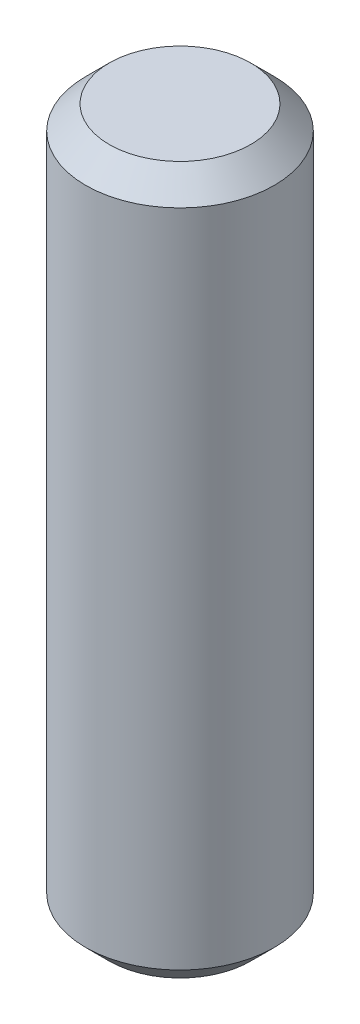
SolidWorks part; units mm, degrees
ref_plane "Front Plane" through (0, 0, 0) normal (0, 0, 1) x (1, 0, 0)
ref_plane "Top Plane" through (0, 0, 0) normal (0, 1, 0) x (1, 0, 0)
ref_plane "Right Plane" through (0, 0, 0) normal (1, 0, 0) x (0, 0, -1)
sketch "Sketch1" plane through (0, 0, 0) normal (0, 1, 0) x (1, 0, 0)
  circle A0 centre (0, 0) radius 4
  dimension "D1" = 8
extrude "Boss-Extrude1" add sketch "Sketch1" along normal mid plane 30
chamfer "Chamfer1" distance 1 angle 45 2 edges at (0, -15, 4) (0, 15, 4)
